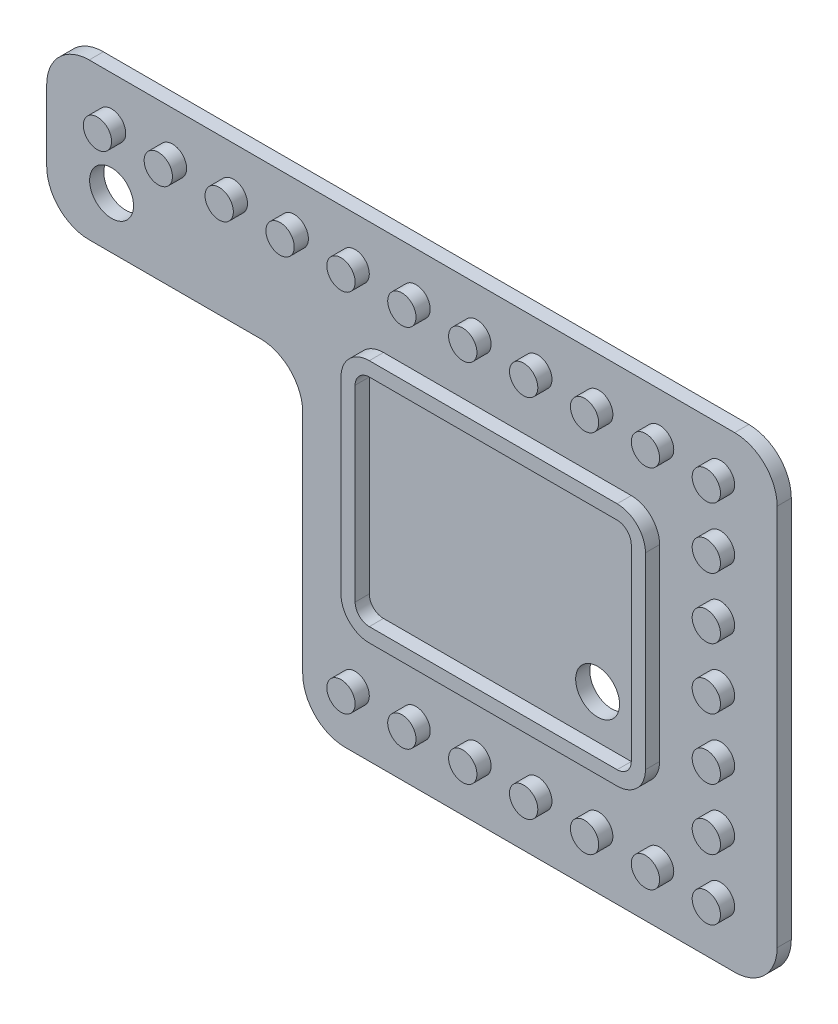
SolidWorks part; units mm, degrees
ref_plane "Front Plane" through (0, 0, 0) normal (0, 0, 1) x (1, 0, 0)
ref_plane "Top Plane" through (0, 0, 0) normal (0, 1, 0) x (1, 0, 0)
ref_plane "Right Plane" through (0, 0, 0) normal (1, 0, 0) x (0, 0, -1)
sketch "Sketch1" plane through (0, 0, 0) normal (0, 0, 1) x (1, 0, 0)
  line L0 (-8, 5) -> (-8, 38)
  line L1 (-8, 38) -> (-59.5805, 38)
  line L2 (-59.5805, 38) -> (-59.5805, 27)
  line L3 (-59.5805, 27) -> (-41.5, 27)
  line L4 (-41.5, 27) -> (-41.5, 5)
  line L5 (-41.5, 5) -> (-8, 5)
  line L6 (-3, 25) -> (-3, 16) construction
  line L7 (-3, 0) -> (-133, 0) construction
  line L8 (-46.5, 22) -> (-89.5, 22) construction
  line L9 (-30, 43) -> (-20, 43) construction
  line L10 (-46.5, 2) -> (-46.5, 22) construction
  dimension "D1" = 5
  dimension "D2" = 5
  dimension "D3" = 5
  dimension "D4" = 5
  dimension "D5" = 5
extrude "Boss-Extrude1" add sketch "Sketch1" along normal blind 1
sketch "Sketch2" plane through (0, 0, 1) normal (0, 0, 1) x (1, 0, 0)
  line L0 (-8, 5) -> (-8, 38) construction
  line L1 (-41.5, 5) -> (-8, 5) construction
  line L2 (-35.8, 29.5) -> (-18.3, 29.5)
  line L3 (-35.8, 30.5) -> (-18.3, 30.5)
  line L4 (-37.8, 28.5) -> (-37.8, 15.236)
  line L5 (-35.8, 13.236) -> (-18.3, 13.236)
  line L6 (-16.3, 28.5) -> (-16.3, 15.236)
  line L7 (-17.3, 28.5) -> (-17.3, 15.236)
  line L8 (-35.8, 14.236) -> (-18.3, 14.236)
  line L9 (-36.8, 28.5) -> (-36.8, 15.236)
  circle A0 centre (-12, 9) radius 1
  circle A1 centre (-12, 13.3) radius 1
  circle A2 centre (-12, 17.6) radius 1
  circle A3 centre (-12, 21.9) radius 1
  circle A4 centre (-12, 26.2) radius 1
  circle A5 centre (-12, 30.5) radius 1
  circle A6 centre (-12, 34.8) radius 1
  circle A7 centre (-16.3, 9) radius 1
  circle A8 centre (-20.6, 9) radius 1
  circle A9 centre (-24.9, 9) radius 1
  circle A10 centre (-29.2, 9) radius 1
  circle A11 centre (-33.5, 9) radius 1
  circle A12 centre (-37.8, 9) radius 1
  circle A13 centre (-16.3, 34.8) radius 1
  circle A14 centre (-20.6, 34.8) radius 1
  circle A15 centre (-24.9, 34.8) radius 1
  circle A16 centre (-29.2, 34.8) radius 1
  circle A17 centre (-33.5, 34.8) radius 1
  circle A18 centre (-37.8, 34.8) radius 1
  circle A19 centre (-42.1, 34.8) radius 1
  circle A20 centre (-46.4, 34.8) radius 1
  circle A21 centre (-50.7, 34.8) radius 1
  circle A22 centre (-55, 34.8) radius 1
  arc A23 (-18.3, 30.5) -> (-16.3, 28.5) centre (-18.3, 28.5) cw
  arc A24 (-16.3, 15.236) -> (-18.3, 13.236) centre (-18.3, 15.236) cw
  arc A25 (-37.8, 15.236) -> (-35.8, 13.236) centre (-35.8, 15.236) ccw
  arc A26 (-37.8, 28.5) -> (-35.8, 30.5) centre (-35.8, 28.5) cw
  arc A27 (-18.3, 29.5) -> (-17.3, 28.5) centre (-18.3, 28.5) cw
  arc A28 (-17.3, 15.236) -> (-18.3, 14.236) centre (-18.3, 15.236) cw
  arc A29 (-36.8, 15.236) -> (-35.8, 14.236) centre (-35.8, 15.236) ccw
  arc A30 (-36.8, 28.5) -> (-35.8, 29.5) centre (-35.8, 28.5) cw
  dimension "D1" = 2
  dimension "D7" = 2
  dimension "D2" = 4
  dimension "D3" = 4
  dimension "D8" = 1
  dimension "D4" = 7
  dimension "D5" = 7
  dimension "D6" = 11
extrude "Boss-Extrude2" add sketch "Sketch2" along normal blind 1
fillet "Fillet1" radius 3 6 edges at (-8, 38, 0.5) (-8, 5, 0.5) (-41.5, 5, 0.5) (-41.5, 27, 0.5) (-59.5805, 27, 0.5) (-59.5805, 38, 0.5)
sketch "Sketch3" plane through (0, 0, 1) normal (0, 0, 1) x (1, 0, 0)
  circle A0 centre (-20.6776, 17.3142) radius 1.55
  circle A1 centre (-55, 30.6513) radius 1.55
  dimension "D1" = 3.1
  dimension "D2" = 3.1
extrude "Cut-Extrude1" cut sketch "Sketch3" against normal up to next
